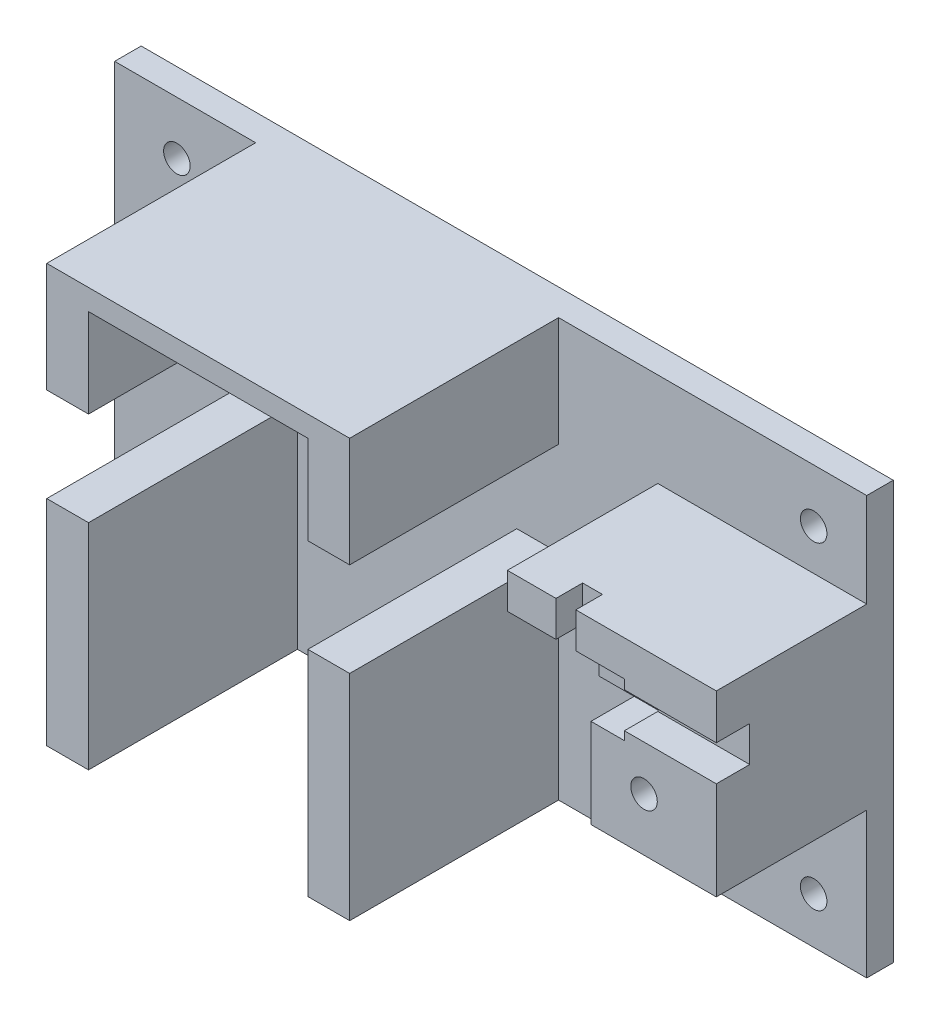
SolidWorks part; units mm, degrees
ref_plane "Front Plane" through (0, 0, 0) normal (0, 0, 1) x (1, 0, 0)
ref_plane "Top Plane" through (0, 0, 0) normal (0, 1, 0) x (1, 0, 0)
ref_plane "Right Plane" through (0, 0, 0) normal (1, 0, 0) x (0, 0, -1)
sketch "Sketch1" plane through (0, 0, 0) normal (0, 0, 1) x (1, 0, 0)
  line L1 (0, 0) -> (180, 0)
  line L2 (0, 0) -> (0, 100)
  line L3 (0, 100) -> (180, 100)
  line L4 (180, 0) -> (180, 100)
  dimension "D1" = 180
  dimension "D2" = 100
extrude "Boss-Extrude1" add sketch "Sketch1" along normal blind 6.35
sketch "Sketch2" plane through (0, 0, 6.35) normal (0, 0, 1) x (1, 0, 0)
  line L1 (96.25, 100) -> (106.25, 100)
  line L2 (96.25, 100) -> (96.25, 73.75)
  line L3 (96.25, 73.75) -> (106.25, 73.75)
  line L4 (106.25, 100) -> (106.25, 73.75)
  line L5 (180, 100) -> (0, 100) construction
  line L6 (0, 0) -> (180, 0) construction
  line L7 (70, 0) -> (70, 100)
  line L8 (96.25, 0) -> (106.25, 0)
  line L9 (96.25, 0) -> (96.25, 51.25)
  line L10 (96.25, 51.25) -> (106.25, 51.25)
  line L11 (106.25, 0) -> (106.25, 51.25)
  line L13 (96.25, 0) -> (96.25, 5)
  line L16 (0, 100) -> (0, 0) construction
  line L19 (70, 5) -> (70, 0)
  line L21 (96.25, 5) -> (96.25, 0)
  line L25 (43.75, 5) -> (43.75, 0)
  line L26 (43.75, 0) -> (43.75, 5)
  line L27 (33.75, 0) -> (33.75, 51.25)
  line L28 (43.75, 51.25) -> (33.75, 51.25)
  line L29 (43.75, 0) -> (43.75, 51.25)
  line L30 (43.75, 0) -> (33.75, 0)
  line L31 (33.75, 100) -> (33.75, 73.75)
  line L32 (43.75, 73.75) -> (33.75, 73.75)
  line L33 (43.75, 100) -> (43.75, 73.75)
  line L34 (43.75, 100) -> (33.75, 100)
  line L35 (43.75, 0) -> (43.75, 5)
  line L37 (43.75, 0) -> (96.25, 0)
  line L38 (43.75, 0) -> (43.75, 5)
  line L40 (96.25, 0) -> (96.25, 5)
  line L41 (43.75, 100) -> (96.25, 100)
  line L42 (43.75, 100) -> (43.75, 95)
  line L43 (43.75, 95) -> (96.25, 95)
  line L44 (96.25, 100) -> (96.25, 95)
  line M10 (0, 0) -> (180, 0)
  line M12 (180, 100) -> (0, 100)
  dimension "D1" = 10
  dimension "D2" = 10
  dimension "D3" = 26.25
  dimension "D4" = 70
  dimension "D5" = 22.5
  dimension "D6" = 26.25
  dimension "D8" = 5
extrude "Boss-Extrude3" add sketch "Sketch2" along normal blind 50 contours L33 L31 L32 M12 | L33 L43 L7 M12 | L7 L43 L2 M12 | L4 L2 L3 M12 | L25 L29 L28 L27 M10 | L11 L10 L9 M10
sketch "Sketch3" plane through (0, 0, 6.35) normal (0, 0, 1) x (1, 0, 0)
  line L0 (180, 0) -> (180, 100) construction
  line L1 (180, 77.5) -> (150, 77.5)
  line L2 (180, 77.5) -> (180, 47.5)
  line L3 (180, 47.5) -> (150, 47.5)
  line L4 (150, 77.5) -> (150, 47.5)
  line L10 (180, 100) -> (106.25, 100) construction
  dimension "D1" = 30
  dimension "D2" = 30
  dimension "D3" = 22.5
extrude "Boss-Extrude4" add sketch "Sketch3" along normal blind 25.65
sketch "Sketch4" plane through (0, 0, 32) normal (0, 0, 1) x (1, 0, 0)
  line L0 (150, 77.5) -> (150, 47.5) construction
  line L1 (150, 69) -> (158, 69)
  line L2 (150, 69) -> (150, 56.2)
  line L3 (150, 56.2) -> (158, 56.2)
  line L4 (158, 69) -> (158, 56.2)
  line L5 (180, 77.5) -> (150, 77.5) construction
  line L6 (150, 69) -> (150, 77.5)
  line L7 (150, 77.5) -> (180, 77.5)
  line L8 (180, 77.5) -> (180, 47.5)
  line L9 (180, 47.5) -> (150, 47.5)
  line L10 (150, 47.5) -> (150, 56.2)
  line L12 (158, 58.25) -> (180, 58.25)
  line L13 (158, 58.25) -> (158, 66.75)
  line L14 (158, 66.75) -> (180, 66.75)
  line L15 (180, 58.25) -> (180, 66.75)
  line M8 (180, 47.5) -> (180, 77.5)
  line M9 (180, 77.5) -> (150, 77.5)
  line M10 (150, 77.5) -> (150, 47.5)
  line M11 (150, 47.5) -> (180, 47.5)
  dimension "D1" = 12.8
  dimension "D2" = 8.5
  dimension "D3" = 8
  dimension "D4" = 8.5
  dimension "D5" = 10.75
extrude "Boss-Extrude5" add sketch "Sketch4" along normal blind 10.35 contours L4 L14 L1 M8 M9 M10 | L12 L4 L3 M10 M11 M8
sketch "Sketch5" plane through (0, 0, 32) normal (0, 0, 1) x (1, 0, 0)
  line L1 (158, 58.25) -> (180, 58.25)
  line L2 (158, 58.25) -> (158, 66.75)
  line L3 (158, 66.75) -> (180, 66.75)
  line L4 (180, 58.25) -> (180, 66.75)
extrude "Boss-Extrude6" add sketch "Sketch5" along normal blind 2.35
sketch "Sketch6" plane through (0, 0, 6.35) normal (0, 0, 1) x (1, 0, 0)
  line L0 (180, 77.5) -> (150, 77.5) construction
  line L1 (150, 69) -> (130, 69)
  line L2 (150, 69) -> (150, 77.5)
  line L3 (150, 77.5) -> (130, 77.5)
  line L4 (130, 69) -> (130, 77.5)
  dimension "D1" = 20
extrude "Boss-Extrude7" add sketch "Sketch6" along normal blind 29.625
sketch "Sketch8" plane through (0, 0, 35.975) normal (0, 0, 1) x (1, 0, 0)
  line L0 (130, 69) -> (150, 69) construction
  line L1 (150, 77.5) -> (146.375, 77.5)
  line L2 (150, 77.5) -> (150, 69)
  line L3 (150, 69) -> (146.375, 69)
  line L4 (146.375, 77.5) -> (146.375, 69)
  line L5 (130, 69) -> (150, 69) construction
  line L6 (130, 77.5) -> (141.625, 77.5)
  line L7 (130, 77.5) -> (130, 69)
  line L8 (130, 69) -> (141.625, 69)
  line L9 (141.625, 77.5) -> (141.625, 69)
  dimension "D1" = 3.625
  dimension "D2" = 4.75
extrude "Boss-Extrude8" add sketch "Sketch8" along normal up to surface (6.375 mm away) up to face at (162.6667, 71.0833, 42.35)
sketch "Sketch9" plane through (0, 0, 6.35) normal (0, 0, 1) x (1, 0, 0)
  line L0 (150, 56.2) -> (158, 56.2) construction
  line L1 (150, 69) -> (141.625, 69)
  line L2 (150, 69) -> (150, 56.2)
  line L3 (150, 56.2) -> (141.625, 56.2)
  line L4 (141.625, 69) -> (141.625, 56.2)
  line L5 (141.625, 69) -> (141.625, 77.5) construction
extrude "Boss-Extrude9" add sketch "Sketch9" along normal up to surface (25.65 mm away) up to face at (154, 62.6, 32)
sketch "Sketch10" plane through (0, 0, 6.35) normal (0, 0, 1) x (1, 0, 0)
  line L0 (33.75, 100) -> (0, 100) construction
  line L4 (180, 77.5) -> (180, 100) construction
  circle A0 centre (14.9, 87.3) radius 3.175
  circle A1 centre (167.3, 87.3) radius 3.175
  circle A2 centre (167.3, 11.1) radius 3.175
  circle A3 centre (14.9, 11.1) radius 3.175
  dimension "D1" = 6.35
  dimension "D2" = 12.7
  dimension "D3" = 12.7
  dimension "D4" = 152.4
  dimension "D5" = 152.4
  dimension "D6" = 76.2
  dimension "D7" = 76.2
extrude "Cut-Extrude1" cut sketch "Sketch10" against normal blind 6.35
sketch "Sketch11" plane through (0, 0, 6.35) normal (0, 0, 1) x (1, 0, 0)
  line L0 (180, 0) -> (180, 47.5) construction
  line L1 (150, 47.5) -> (180, 47.5)
  line L2 (150, 47.5) -> (150, 34.8)
  line L3 (150, 34.8) -> (180, 34.8)
  line L4 (180, 47.5) -> (180, 34.8)
  dimension "D1" = 12.7
extrude "Boss-Extrude10" add sketch "Sketch11" along normal up to surface (36 mm away) up to face at (162.6667, 53.9833, 42.35)
sketch "Sketch12" plane through (0, 0, 42.35) normal (0, 0, 1) x (1, 0, 0)
  line L0 (180, 77.5) -> (146.375, 77.5) construction
  line L1 (180, 34.8) -> (150, 34.8)
  line L2 (180, 34.8) -> (180, 77.5)
  line L3 (180, 77.5) -> (150, 77.5)
  line L4 (150, 34.8) -> (150, 77.5)
  line L10 (146.375, 69) -> (158, 69) construction
  line L11 (130, 77.5) -> (150, 77.5)
  line L12 (130, 77.5) -> (130, 69)
  line L13 (130, 69) -> (150, 69)
  line L14 (150, 77.5) -> (150, 69)
  circle A0 centre (162.7, 47.5) radius 3.175
  dimension "D1" = 6.35
  dimension "D2" = 12.7
  dimension "D3" = 12.7
extrude "Cut-Extrude2" cut sketch "Sketch12" against normal blind 10 contours A0
